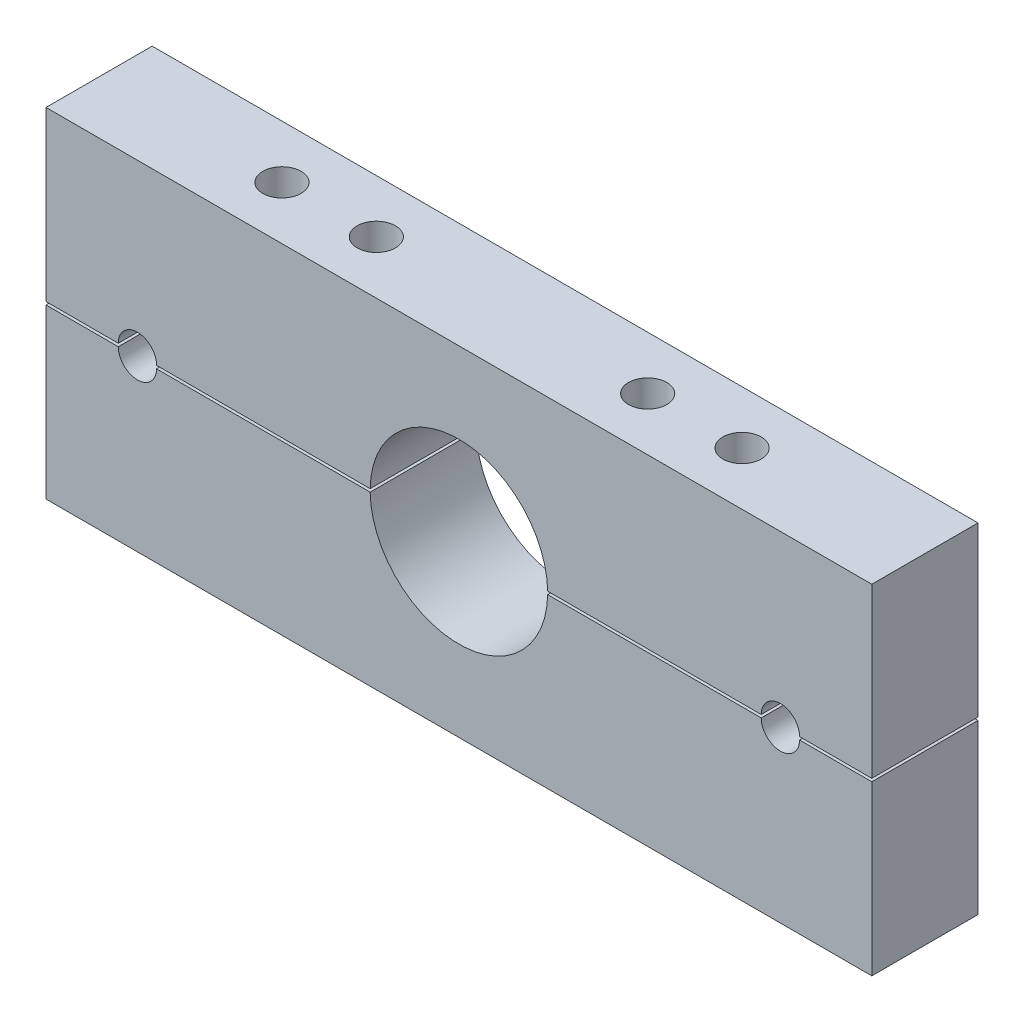
SolidWorks part; units mm, degrees
ref_plane "Plano frontal" through (0, 0, 0) normal (0, 0, 1) x (1, 0, 0)
ref_plane "Plano superior" through (0, 0, 0) normal (0, 1, 0) x (1, 0, 0)
ref_plane "Plano direito" through (0, 0, 0) normal (1, 0, 0) x (0, 0, -1)
sketch "Sketch1" plane through (0, 0, 0) normal (0, 0, 1) x (1, 0, 0)
  line L0 (81.8295, -84.5197) -> (81.8295, -142.0197) construction
  line L1 (-12.1705, -84.5197) -> (267.8295, -84.5197)
  line L2 (-12.1705, -84.5197) -> (-12.1705, -142.0197)
  line L3 (-12.1705, -142.0197) -> (267.8295, -142.0197)
  line L4 (267.8295, -84.5197) -> (267.8295, -142.0197)
  line L5 (49.8295, -84.5197) -> (49.8295, -142.0197) construction
  line L6 (18.8295, -142.0197) -> (18.8295, -84.5197) construction
  line L7 (236.8295, -84.5197) -> (236.8295, -142.0197) construction
  circle A0 centre (127.8295, -142.0197) radius 30.1
  circle A1 centre (18.8295, -142.0197) radius 6.5
  circle A2 centre (236.8295, -142.0197) radius 6.5
  dimension "D1" = 60.2
  dimension "D6" = 13
  dimension "D2" = 57.5
  dimension "D3" = 32
  dimension "D4" = 62
  dimension "D5" = 280
  dimension "D7" = 31
  dimension "D8" = 31
extrude "Boss-Extrude1" add sketch "Sketch1" along normal blind 36 contours A2 L3 L4 L1 L2 A1 A0 | L3 A2 | L3 A1
sketch "Sketch4" plane through (0, -84.5197, 0) normal (0, 1, 0) x (1, 0, 0)
  line L0 (49.8295, 0) -> (49.8295, -36) construction
  line L1 (-12.1705, -36) -> (267.8295, -36) construction
  line L2 (81.8295, 0) -> (81.8295, -36) construction
  line L3 (-12.1705, -18) -> (49.8295, -18) construction
  line L4 (-12.1705, -36) -> (-12.1705, 0) construction
  line L5 (49.8295, -18) -> (81.8295, -18) construction
  line L6 (267.8295, -18) -> (205.8295, -18) construction
  line L7 (267.8295, -36) -> (267.8295, 0) construction
  line L8 (205.8295, -18) -> (173.8295, -18) construction
  circle A0 centre (205.8295, -18) radius 6.5
  circle A1 centre (173.8295, -18) radius 6.5
  circle A2 centre (81.8295, -18) radius 6.5
  circle A3 centre (49.8295, -18) radius 6.5
  dimension "D1" = 13
extrude "Cut-Extrude3" cut sketch "Sketch4" against normal through all
mirror "Mirror1" about plane through (0, -142.0197, 36) normal (0, 1, 0) of "Boss-Extrude1", "Cut-Extrude3"
sketch "Sketch5" plane through (-12.1705, 0, 0) normal (-1, 0, 0) x (0, 0, 1)
  line L0 (0, -84.5197) -> (0, -199.5197) construction
  line L1 (0, -141.5197) -> (36, -141.5197)
  line L2 (0, -141.5197) -> (0, -142.5197)
  line L3 (0, -142.5197) -> (36, -142.5197)
  line L4 (36, -141.5197) -> (36, -142.5197)
  line L5 (36, -84.5197) -> (36, -199.5197) construction
  line L6 (0, -142.0197) -> (36, -142.0197) construction
  line L7 (36, -142.0197) -> (36, -84.5197) construction
  line L8 (36, -142.0197) -> (36, -199.5197) construction
  dimension "D1" = 1
extrude "Cut-Extrude5" cut sketch "Sketch5" against normal through all
sketch "Sketch3" plane through (0, 0, 36) normal (0, 0, 1) x (1, 0, 0)
  line L1 (267.8295, -141.5197) -> (157.9253, -141.5197) construction
  line L2 (18.8295, -142.0197) -> (18.8295, -84.5197) construction
  line L3 (236.8295, -84.5197) -> (236.8295, -142.0197) construction
  line L4 (97.7337, -141.5197) -> (-12.1705, -141.5197) construction
  line L5 (12.3295, -141.5197) -> (243.3295, -141.5197)
  line L6 (97.7337, -142.5197) -> (-12.1705, -142.5197) construction
  line L7 (267.8295, -142.5197) -> (157.9253, -142.5197) construction
  line L8 (12.3295, -142.5197) -> (243.3295, -142.5197)
  arc A0 (25.3295, -141.5197) -> (12.3295, -141.5197) centre (18.8295, -141.5197) ccw
  arc A1 (243.3295, -141.5197) -> (230.3295, -141.5197) centre (236.8295, -141.5197) ccw
  arc A2 (12.3295, -142.5197) -> (25.3295, -142.5197) centre (18.8295, -142.5197) ccw
  arc A3 (230.3295, -142.5197) -> (243.3295, -142.5197) centre (236.8295, -142.5197) ccw
  dimension "D1" = 13
extrude "Cut-Extrude6" cut sketch "Sketch3" against normal through all contours A0 M12 | L8 A2 | L5 A1 | L8 A3
